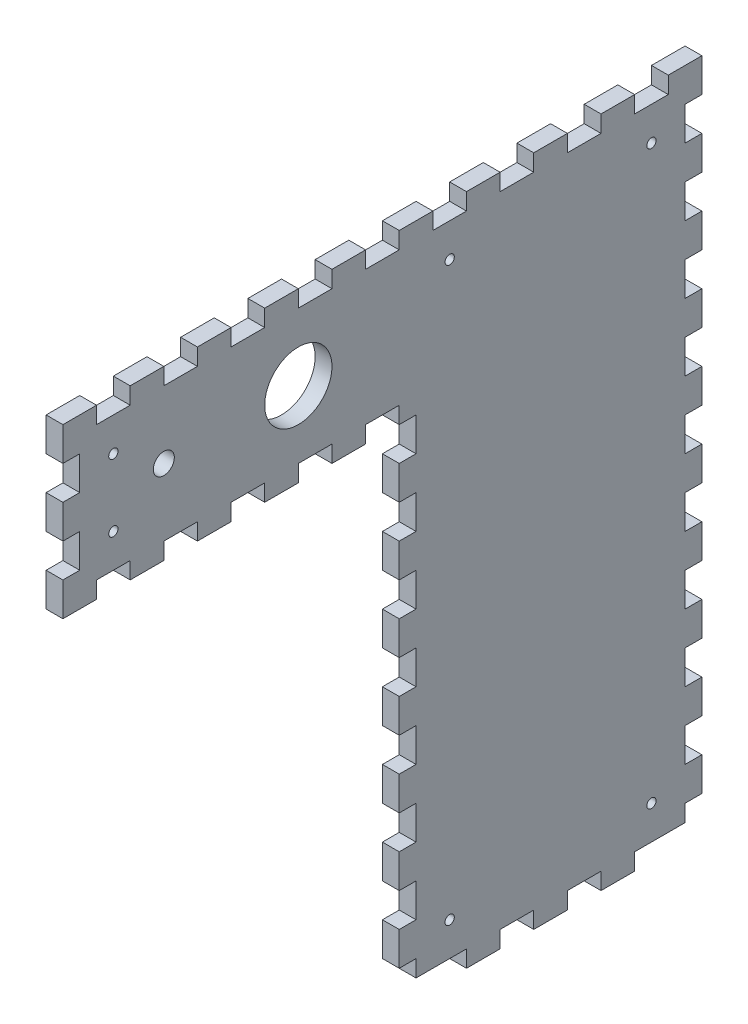
SolidWorks part; units mm, degrees
material "Pine"
ref_plane "Front Plane" through (0, 0, 0) normal (0, 0, 1) x (1, 0, 0)
ref_plane "Top Plane" through (0, 0, 0) normal (0, 1, 0) x (1, 0, 0)
ref_plane "Right Plane" through (0, 0, 0) normal (1, 0, 0) x (0, 0, -1)
sketch "Sketch1" plane through (0, 0, 0) normal (1, 0, 0) x (0, 0, -1)
  line L0 (0, 0) -> (0, 190.5)
  line L1 (0, 190.5) -> (-127, 190.5)
  line L2 (-127, 190.5) -> (-127, 254)
  line L3 (-127, 254) -> (114.3, 254)
  line L4 (114.3, 254) -> (114.3, 0)
  line L5 (114.3, 0) -> (0, 0)
  line L7 (-107.95, 234.95) -> (95.25, 234.95) construction
  line L8 (-107.95, 234.95) -> (-107.95, 209.55) construction
  line L9 (-107.95, 209.55) -> (95.25, 209.55) construction
  line L10 (95.25, 234.95) -> (95.25, 209.55) construction
  line L11 (95.25, 234.95) -> (19.05, 234.95) construction
  line L12 (95.25, 234.95) -> (95.25, 19.05) construction
  line L13 (95.25, 19.05) -> (19.05, 19.05) construction
  line L14 (19.05, 234.95) -> (19.05, 19.05) construction
  circle A0 centre (-107.95, 234.95) radius 1.75
  circle A1 centre (-107.95, 209.55) radius 1.75
  circle A2 centre (19.05, 234.95) radius 1.75
  circle A3 centre (95.25, 234.95) radius 1.75
  circle A4 centre (19.05, 19.05) radius 1.75
  circle A5 centre (95.25, 19.05) radius 1.75
  dimension "D11" = 3.5
  dimension "D1" = 114.3
  dimension "D2" = 254
  dimension "D3" = 241.3
  dimension "D4" = 63.5
  dimension "D5" = 25.4
  dimension "D6" = 76.2
  dimension "D7" = 190.5
  dimension "D8" = 127
  dimension "D9" = 19.05
  dimension "D10" = 19.05
extrude "Boss-Extrude1" add sketch "Sketch1" along normal blind 6.35
sketch "Sketch2" plane through (6.35, 0, 0) normal (1, 0, 0) x (0, 0, -1)
  line L0 (114.3, 254) -> (-127, 254) construction
  line L1 (-114.3, 254) -> (-101.6, 254)
  line L2 (-114.3, 254) -> (-114.3, 247.65)
  line L3 (-114.3, 247.65) -> (-101.6, 247.65)
  line L4 (-101.6, 254) -> (-101.6, 247.65)
  line L5 (-127, 254) -> (-127, 190.5) construction
  dimension "D1" = 12.7
  dimension "D2" = 6.35
  dimension "D3" = 12.7
extrude "Cut-Extrude1" cut sketch "Sketch2" against normal through all
pattern_linear "LPattern1" count 10 spacing 25.4 along (0, 0, -1) of "Cut-Extrude1"
sketch "Sketch3" plane through (6.35, 0, 0) normal (1, 0, 0) x (0, 0, -1)
  line L0 (114.3, 0) -> (114.3, 254) construction
  line L1 (114.3, 241.3) -> (107.95, 241.3)
  line L2 (114.3, 241.3) -> (114.3, 228.6)
  line L3 (114.3, 228.6) -> (107.95, 228.6)
  line L4 (107.95, 241.3) -> (107.95, 228.6)
  line L5 (114.3, 254) -> (101.6, 254) construction
  line L6 (101.6, 247.65) -> (101.6, 254) construction
  line L7 (88.9, 247.65) -> (101.6, 247.65) construction
  dimension "D1" = 12.7
extrude "Cut-Extrude2" cut sketch "Sketch3" against normal through all
pattern_linear "LPattern2" count 10 spacing 25.4 along (0, -1, 0) of "Cut-Extrude2"
sketch "Sketch4" plane through (6.35, 0, 0) normal (1, 0, 0) x (0, 0, -1)
  line L0 (-127, 254) -> (-127, 190.5) construction
  line L1 (-127, 241.3) -> (-120.65, 241.3)
  line L2 (-127, 241.3) -> (-127, 228.6)
  line L3 (-127, 228.6) -> (-120.65, 228.6)
  line L4 (-120.65, 241.3) -> (-120.65, 228.6)
  line L5 (-114.3, 254) -> (-127, 254) construction
  line L6 (-127, 215.9) -> (-120.65, 215.9)
  line L7 (-127, 215.9) -> (-127, 203.2)
  line L8 (-127, 203.2) -> (-120.65, 203.2)
  line L9 (-120.65, 215.9) -> (-120.65, 203.2)
  line L10 (-114.3, 247.65) -> (-101.6, 247.65) construction
  dimension "D1" = 12.7
  dimension "D2" = 12.7
  dimension "D3" = 6.35
extrude "Cut-Extrude3" cut sketch "Sketch4" against normal through all
sketch "Sketch5" plane through (6.35, 0, 0) normal (1, 0, 0) x (0, 0, -1)
  line L0 (-127, 190.5) -> (0, 190.5) construction
  line L1 (-114.3, 190.5) -> (-101.6, 190.5)
  line L2 (-114.3, 190.5) -> (-114.3, 196.85)
  line L3 (-114.3, 196.85) -> (-101.6, 196.85)
  line L4 (-101.6, 190.5) -> (-101.6, 196.85)
  line L5 (-127, 203.2) -> (-127, 190.5) construction
  line L6 (-114.3, 247.65) -> (-101.6, 247.65) construction
  line L7 (-127, 203.2) -> (-120.65, 203.2) construction
  dimension "D1" = 12.7
extrude "Cut-Extrude4" cut sketch "Sketch5" against normal through all
pattern_linear "LPattern3" count 5 spacing 25.4 along (0, 0, -1) of "Cut-Extrude4"
sketch "Sketch6" plane through (6.35, 0, 0) normal (1, 0, 0) x (0, 0, -1)
  line L0 (114.3, 12.7) -> (107.95, 12.7) construction
  line L1 (0, 0) -> (6.35, 0)
  line L2 (0, 0) -> (0, 12.7)
  line L3 (0, 12.7) -> (6.35, 12.7)
  line L4 (6.35, 0) -> (6.35, 12.7)
extrude "Cut-Extrude5" cut sketch "Sketch6" against normal through all
pattern_linear "LPattern4" count 8 spacing 25.4 along (0, 1, 0) of "Cut-Extrude5"
sketch "Sketch7" plane through (6.35, 0, 0) normal (1, 0, 0) x (0, 0, -1)
  line L0 (6.35, 0) -> (107.95, 0) construction
  line L1 (12.7, 0) -> (25.4, 0)
  line L2 (12.7, 0) -> (12.7, 6.35)
  line L3 (12.7, 6.35) -> (25.4, 6.35)
  line L4 (25.4, 0) -> (25.4, 6.35)
  line L5 (6.35, 0) -> (6.35, 12.7) construction
  line L6 (38.1, 0) -> (50.8, 0)
  line L7 (38.1, 0) -> (38.1, 6.35)
  line L8 (38.1, 6.35) -> (50.8, 6.35)
  line L9 (50.8, 0) -> (50.8, 6.35)
  line L10 (63.5, 0) -> (76.2, 0)
  line L11 (63.5, 0) -> (63.5, 6.35)
  line L12 (63.5, 6.35) -> (76.2, 6.35)
  line L13 (76.2, 0) -> (76.2, 6.35)
  line L14 (6.35, 12.7) -> (0, 12.7) construction
  line L16 (88.9, 0) -> (101.6, 0)
  line L17 (88.9, 0) -> (88.9, 6.35)
  line L18 (88.9, 6.35) -> (101.6, 6.35)
  line L19 (101.6, 0) -> (101.6, 6.35)
  dimension "D1" = 6.35
  dimension "D2" = 12.7
  dimension "D3" = 12.7
  dimension "D4" = 12.7
extrude "Cut-Extrude6" cut sketch "Sketch7" against normal through all
sketch "Sketch8" plane through (6.35, 0, 0) normal (1, 0, 0) x (0, 0, -1)
  line L1 (12.7, 6.35) -> (6.35, 6.35)
  line L2 (12.7, 6.35) -> (12.7, 0)
  line L3 (12.7, 0) -> (6.35, 0)
  line L4 (6.35, 6.35) -> (6.35, 0)
  line L5 (101.6, 6.35) -> (107.95, 6.35)
  line L6 (101.6, 6.35) -> (101.6, 0)
  line L7 (101.6, 0) -> (107.95, 0)
  line L8 (107.95, 6.35) -> (107.95, 0)
extrude "Cut-Extrude7" cut sketch "Sketch8" against normal through all
sketch "Sketch9" plane through (6.35, 0, 0) normal (1, 0, 0) x (0, 0, -1)
  line L0 (-101.6, 190.5) -> (-88.9, 190.5) construction
  line L1 (-127, 228.6) -> (-127, 215.9) construction
  circle A0 centre (-88.9, 222.25) radius 3.9687
  dimension "D1" = 7.9375
  dimension "D2" = 31.75
  dimension "D3" = 38.1
extrude "Cut-Extrude8" cut sketch "Sketch9" against normal through all
sketch "Sketch10" plane through (6.35, 0, 0) normal (1, 0, 0) x (0, 0, -1)
  line L0 (-88.9, 222.25) -> (-38.1, 222.25) construction
  circle A0 centre (-38.1, 222.25) radius 12.7
  dimension "D1" = 25.4
  dimension "D2" = 50.8
extrude "Cut-Extrude9" cut sketch "Sketch10" against normal through all
